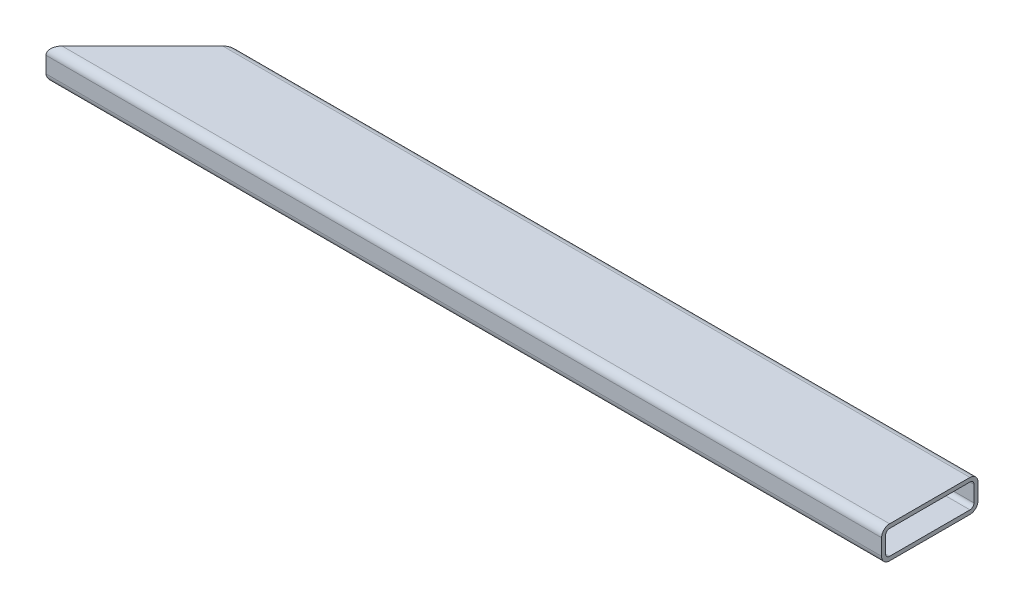
SolidWorks part; units mm, degrees
material "Alloy Steel"
ref_plane "Front Plane" through (0, 0, 0) normal (0, 0, 1) x (1, 0, 0)
ref_plane "Top Plane" through (0, 0, 0) normal (0, 1, 0) x (1, 0, 0)
ref_plane "Right Plane" through (0, 0, 0) normal (1, 0, 0) x (0, 0, -1)
sketch "Sketch1" plane through (0, 0, 0) normal (1, 0, 0) x (0, 0, -1)
  line L1 (0, 0) -> (76.2, 0)
  line L2 (0, 0) -> (0, 25.4)
  line L3 (0, 25.4) -> (76.2, 25.4)
  line L4 (76.2, 0) -> (76.2, 25.4)
  dimension "D1" = 25.4
  dimension "D2" = 76.2
extrude "Boss-Extrude1" add sketch "Sketch1" along normal blind 660.4
fillet "Fillet1" radius 6.35 4 edges at (330.2, 0, -76.2) (330.2, 25.4, -76.2) (330.2, 0, 0) (330.2, 25.4, 0)
shell "Shell1" thickness 3.175
sketch "Sketch2" plane through (0, 25.4, 0) normal (0, 1, 0) x (1, 0, 0)
  line L0 (0, 0) -> (76.2, 76.2)
  line L1 (0, 76.2) -> (660.4, 76.2) construction
  line L2 (76.2, 76.2) -> (0, 76.2)
  line L3 (0, 76.2) -> (0, 0)
  line L4 (660.4, 0) -> (0, 0) construction
  dimension "D1" = 45
extrude "Cut-Extrude1" cut sketch "Sketch2" against normal blind 25.4
